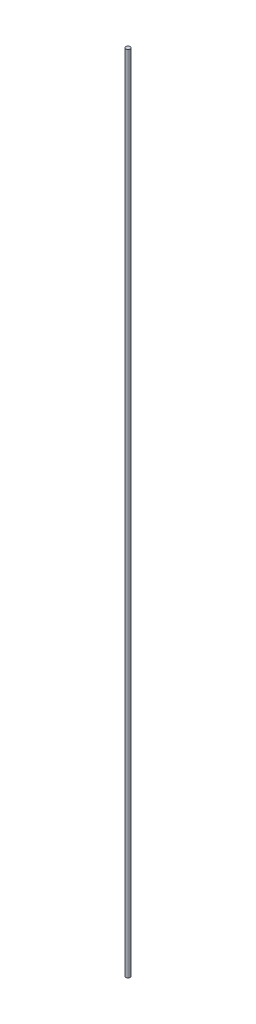
SolidWorks part; units mm, degrees
ref_plane "Plano frontal" through (0, 0, 0) normal (0, 0, 1) x (1, 0, 0)
ref_plane "Plano superior" through (0, 0, 0) normal (0, 1, 0) x (1, 0, 0)
ref_plane "Plano direito" through (0, 0, 0) normal (1, 0, 0) x (0, 0, -1)
sketch "Esboço1" plane through (0, 0, 0) normal (0, 1, 0) x (1, 0, 0)
  circle A0 centre (0, 0) radius 3
  dimension "D1" = 6
extrude "Ressalto-extrusão1" add sketch "Esboço1" along normal blind 1124
